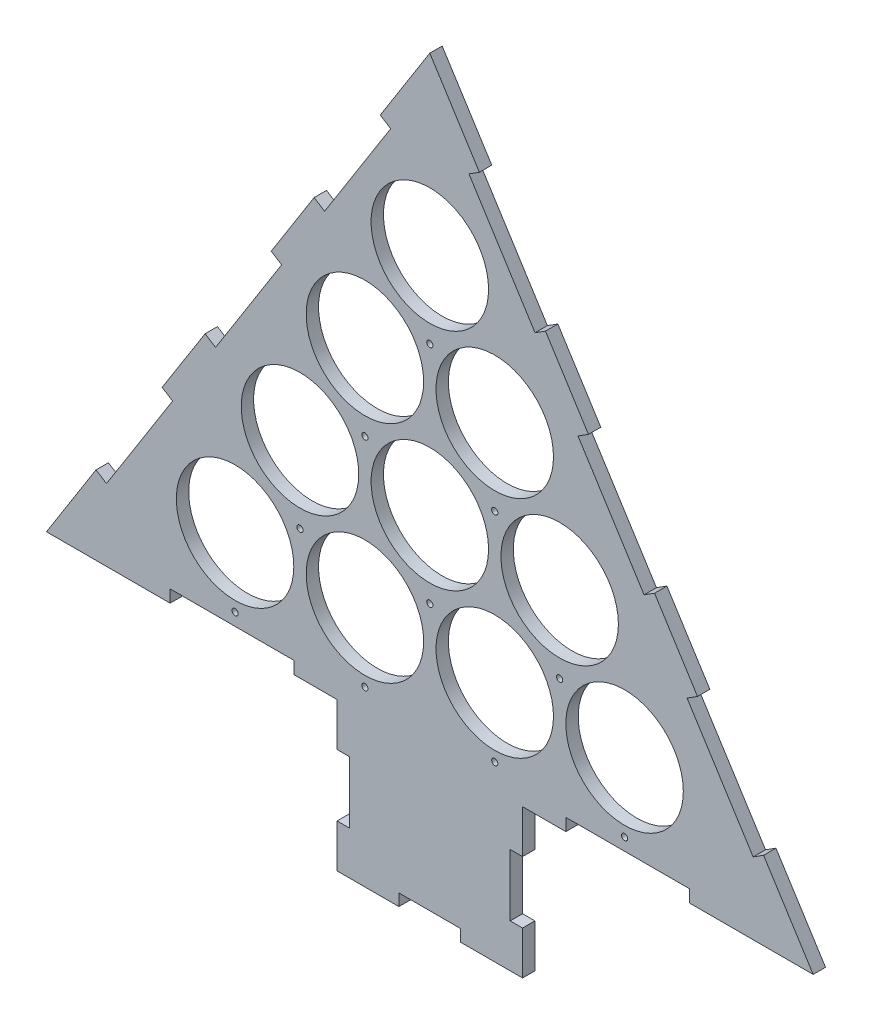
SolidWorks part; units mm, degrees
ref_plane "Plan de face" through (0, 0, 0) normal (0, 0, 1) x (1, 0, 0)
ref_plane "Plan de dessus" through (0, 0, 0) normal (0, 1, 0) x (1, 0, 0)
ref_plane "Plan de droite" through (0, 0, 0) normal (1, 0, 0) x (0, 0, -1)
sketch "Esquisse1" plane through (0, 0, 0) normal (0, 0, 1) x (1, 0, 0)
  line L0 (0, 0) -> (-371.1464, 0) construction
  line L1 (0, 0) -> (478.5179, 0) construction
  line L2 (0, 0) -> (0, 90.9327) construction
  line L3 (0, 90.9327) -> (-157.5, 90.9327) construction
  line L4 (0, 90.9327) -> (157.5, 90.9327) construction
  line L5 (0, 90.9327) -> (0, 181.8653) construction
  line L6 (0, 181.8653) -> (-52.5, 181.8653) construction
  line L7 (0, 181.8653) -> (52.5, 181.8653) construction
  line L8 (0, 181.8653) -> (0, 363.4062) construction
  line L9 (-310, -75.6429) -> (0, 414.5612)
  line L10 (0, 414.5612) -> (310, -75.6429)
  line L11 (310, -75.6429) -> (-310, -75.6429)
  circle A0 centre (-157.5, 0) radius 47.5
  circle A1 centre (-52.5, 0) radius 47.5
  circle A2 centre (52.5, 0) radius 47.5
  circle A3 centre (157.5, 0) radius 47.5
  circle A4 centre (-105, 90.9327) radius 47.5
  circle A5 centre (0, 90.9327) radius 47.5
  circle A6 centre (105, 90.9327) radius 47.5
  circle A7 centre (-52.5, 181.8653) radius 47.5
  circle A8 centre (52.5, 181.8653) radius 47.5
  circle A9 centre (0, 272.798) radius 47.5
  dimension "D1" = 95
  dimension "D2" = 95
  dimension "D3" = 95
  dimension "D4" = 95
  dimension "D5" = 105
  dimension "D6" = 52.5
  dimension "D7" = 52.5
  dimension "D8" = 105
  dimension "D9" = 95
  dimension "D10" = 95
  dimension "D11" = 95
  dimension "D12" = 105
  dimension "D13" = 105
  dimension "D14" = 105
  dimension "D15" = 95
  dimension "D16" = 95
  dimension "D17" = 105
  dimension "D18" = 52.5
  dimension "D19" = 52.5
  dimension "D20" = 95
  dimension "D21" = 105
  dimension "D22" = 80
  dimension "D23" = 620
  dimension "D24" = 580
  dimension "D25" = 0
  dimension "D26" = 580
extrude "Boss.-Extru.1" add sketch "Esquisse1" along normal blind 10
sketch "Esquisse3" plane through (0, 0, 10) normal (0, 0, 1) x (1, 0, 0)
  line L10 (-269.9138, -12.2544) -> (-261.462, -17.5992)
  line L15 (0, 414.5612) -> (-310, -75.6429) construction
  line L16 (-261.462, -17.5992) -> (-208.0137, 66.9187)
  line L17 (-208.0137, 66.9187) -> (-216.4655, 72.2635)
  line L18 (-216.4655, 72.2635) -> (-269.9138, -12.2544)
  line L19 (-181.7241, 127.2002) -> (-173.2723, 121.8554)
  line L20 (-173.2723, 121.8554) -> (-119.8241, 206.3733)
  line L21 (-119.8241, 206.3733) -> (-128.2759, 211.7181)
  line L22 (-128.2759, 211.7181) -> (-181.7241, 127.2002)
  line L23 (-93.5345, 266.6548) -> (-85.0827, 261.31)
  line L24 (-85.0827, 261.31) -> (-31.6344, 345.8279)
  line L25 (-31.6344, 345.8279) -> (-40.0862, 351.1727)
  line L26 (-40.0862, 351.1727) -> (-93.5345, 266.6548)
  line L27 (269.9138, -12.2544) -> (261.462, -17.5992)
  line L28 (310, -75.6429) -> (0, 414.5612) construction
  line L29 (261.462, -17.5992) -> (208.0137, 66.9187)
  line L30 (208.0137, 66.9187) -> (216.4655, 72.2635)
  line L31 (216.4655, 72.2635) -> (269.9138, -12.2544)
  line L32 (181.7241, 127.2002) -> (173.2723, 121.8554)
  line L33 (173.2723, 121.8554) -> (119.8241, 206.3733)
  line L34 (119.8241, 206.3733) -> (128.2759, 211.7181)
  line L35 (128.2759, 211.7181) -> (181.7241, 127.2002)
  line L36 (93.5345, 266.6548) -> (85.0827, 261.31)
  line L37 (85.0827, 261.31) -> (31.6344, 345.8279)
  line L38 (31.6344, 345.8279) -> (40.0862, 351.1727)
  line L39 (40.0862, 351.1727) -> (93.5345, 266.6548)
  line L40 (-310, -75.6429) -> (310, -75.6429) construction
  line L41 (-210, -75.6429) -> (-110, -75.6429)
  line L42 (-210, -75.6429) -> (-210, -65.6429)
  line L43 (-210, -65.6429) -> (-110, -65.6429)
  line L44 (-110, -75.6429) -> (-110, -65.6429)
  line L45 (0, 0) -> (0, -75.6429) construction
  line L46 (210, -65.6429) -> (110, -65.6429)
  line L47 (110, -75.6429) -> (110, -65.6429)
  line L48 (210, -75.6429) -> (110, -75.6429)
  line L49 (210, -75.6429) -> (210, -65.6429)
  dimension "D3" = 100
  dimension "D4" = 10
  dimension "D5" = 100
  dimension "D10" = 10
  dimension "D11" = 100
  dimension "D12" = 10
  dimension "D13" = 100
  dimension "D14" = 10
  dimension "D15" = 100
  dimension "D16" = 75
  dimension "D17" = 75
  dimension "D18" = 65
  dimension "D19" = 100
  dimension "D20" = 10
  dimension "D21" = 10
  dimension "D22" = 100
  dimension "D23" = 75
  dimension "D24" = 65
  dimension "D25" = 100
  dimension "D26" = 10
  dimension "D27" = 75
extrude "Enlèv. mat.-Extru.1" cut sketch "Esquisse3" against normal through all
sketch "Esquisse4" plane through (0, 0, 10) normal (0, 0, 1) x (1, 0, 0)
  line L0 (-110, -65.6429) -> (-210, -65.6429) construction
  circle A0 centre (-157.5, -55.6429) radius 2.5
  circle A3 centre (-52.5, -55.6429) radius 2.5
  circle A4 centre (52.5, -55.6429) radius 2.5
  circle A5 centre (157.5, -55.6429) radius 2.5
  circle A6 centre (-105, 29.0474) radius 2.5
  circle A8 centre (-157.5, 0) radius 47.5 construction
  circle A10 centre (-52.5, 0) radius 47.5 construction
  circle A12 centre (0, 29.0474) radius 2.5
  circle A13 centre (105, 29.0474) radius 2.5
  circle A14 centre (-52.5, 119.98) radius 2.5
  circle A15 centre (-105, 90.9327) radius 47.5 construction
  circle A16 centre (0, 90.9327) radius 47.5 construction
  circle A17 centre (52.5, 119.98) radius 2.5
  circle A18 centre (0, 210.9127) radius 2.5
  circle A19 centre (52.5, 181.8653) radius 47.5 construction
  circle A20 centre (-52.5, 181.8653) radius 47.5 construction
  dimension "D1" = 5
  dimension "D2" = 10
  dimension "D3" = 4
  dimension "D4" = 5
  dimension "D5" = 60
  dimension "D6" = 60
  dimension "D7" = 3
  dimension "D8" = 5
  dimension "D9" = 60
  dimension "D10" = 60
  dimension "D12" = 5
  dimension "D13" = 60
  dimension "D14" = 60
  dimension "D11" = 2
extrude "Enlèv. mat.-Extru.2" cut sketch "Esquisse4" against normal through all
sketch "Esquisse6" plane through (0, 0, 10) normal (0, 0, 1) x (1, 0, 0)
  line L0 (-110, -75.6429) -> (110, -75.6429) construction
  line L1 (-75, -75.6429) -> (75, -75.6429)
  line L2 (-75, -75.6429) -> (-75, -195.6429)
  line L3 (-75, -195.6429) -> (75, -195.6429)
  line L4 (75, -75.6429) -> (75, -195.6429)
  dimension "D1" = 150
  dimension "D2" = 120
  dimension "D3" = 75
extrude "Boss.-Extru.2" add sketch "Esquisse6" against normal blind 10
sketch "Esquisse7" plane through (0, 0, 10) normal (0, 0, 1) x (1, 0, 0)
  line L0 (-75, -75.6429) -> (-75, -195.6429) construction
  line L1 (-75, -110.6429) -> (-65, -110.6429)
  line L2 (-75, -110.6429) -> (-75, -160.6429)
  line L3 (-75, -160.6429) -> (-65, -160.6429)
  line L4 (-65, -110.6429) -> (-65, -160.6429)
  line L5 (-75, -195.6429) -> (75, -195.6429) construction
  line L6 (-25, -195.6429) -> (25, -195.6429)
  line L7 (-25, -195.6429) -> (-25, -186.0721)
  line L8 (-25, -186.0721) -> (25, -186.0721)
  line L9 (25, -195.6429) -> (25, -186.0721)
  line L10 (75, -195.6429) -> (75, -75.6429) construction
  line L11 (75, -160.6429) -> (65, -160.6429)
  line L12 (75, -160.6429) -> (75, -110.6429)
  line L13 (75, -110.6429) -> (65, -110.6429)
  line L14 (65, -160.6429) -> (65, -110.6429)
  line L15 (75, -75.6429) -> (110, -75.6429) construction
  line L16 (-110, -75.6429) -> (-75, -75.6429) construction
  dimension "D1" = 10
  dimension "D2" = 10
  dimension "D3" = 50
  dimension "D4" = 50
  dimension "D5" = 35
  dimension "D6" = 35
  dimension "D7" = 50
  dimension "D8" = 50
extrude "Enlèv. mat.-Extru.3" cut sketch "Esquisse7" against normal blind 10
